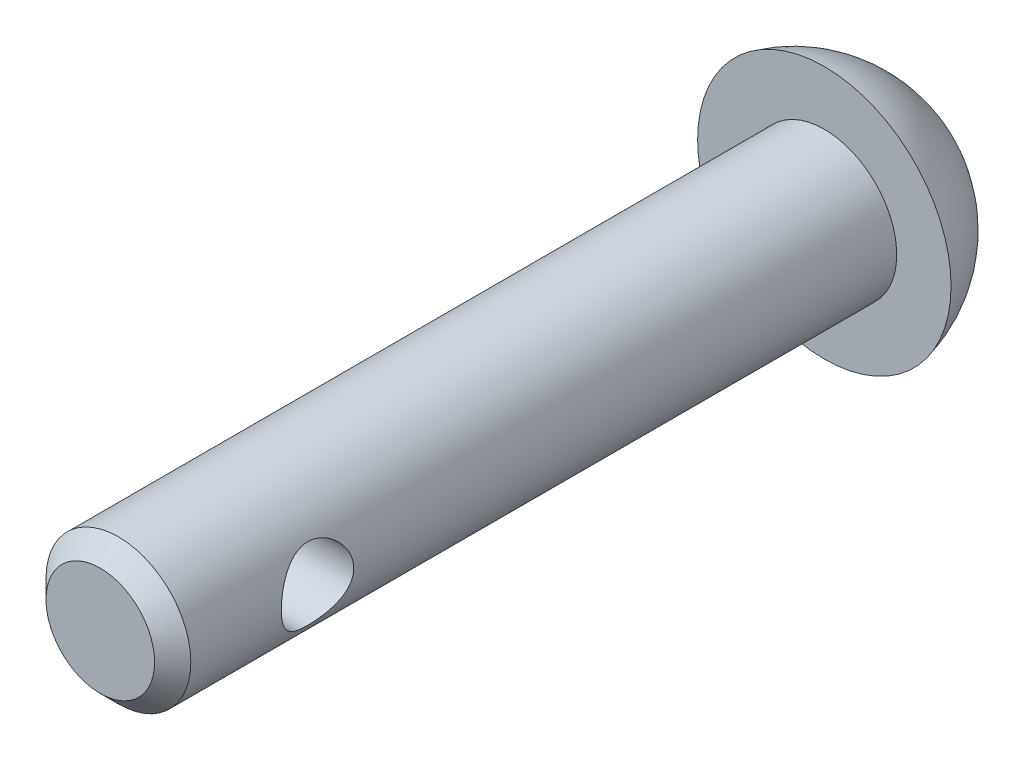
SolidWorks part; units mm, degrees
ref_plane "Front Plane" through (0, 0, 0) normal (0, 0, 1) x (1, 0, 0)
ref_plane "Top Plane" through (0, 0, 0) normal (0, 1, 0) x (1, 0, 0)
ref_plane "Right Plane" through (0, 0, 0) normal (1, 0, 0) x (0, 0, -1)
sketch "Sketch2" plane through (0, 0, 0) normal (0, 0, 1) x (1, 0, 0)
  circle A0 centre (0, 0) radius 2
  dimension "D1" = 4
extrude "Boss-Extrude1" add sketch "Sketch2" along normal mid plane 20
chamfer "Chamfer1" distance 0.5 angle 45 1 edges at (2, 0, 10)
sketch "Sketch3" plane through (0, 0, 0) normal (1, 0, 0) x (0, 0, -1)
  line L0 (6.0053, 0) -> (16.4706, 0) construction
  line L1 (10, 0) -> (10, 3.5)
  line L2 (10, -2) -> (10, 2) construction
  line L3 (10, 0) -> (12.7574, 0)
  arc A0 (10, 3.5) -> (12.7574, 0) centre (9.1574, 0) cw
  point P9 (0, 0)
  dimension "D2" = 3.6
  dimension "D1" = 3.5
revolve "Revolve1" add sketch "Sketch3" angle 360 about L0
sketch "Sketch4" plane through (0, 0, 0) normal (1, 0, 0) x (0, 0, -1)
  line L0 (10, 3.5) -> (10, -3.5) construction
  circle A0 centre (-6, 0) radius 1
  point P4 (0, 0)
  dimension "D1" = 2
  dimension "D2" = 16
extrude "Cut-Extrude1" cut sketch "Sketch4" against normal mid plane 20
